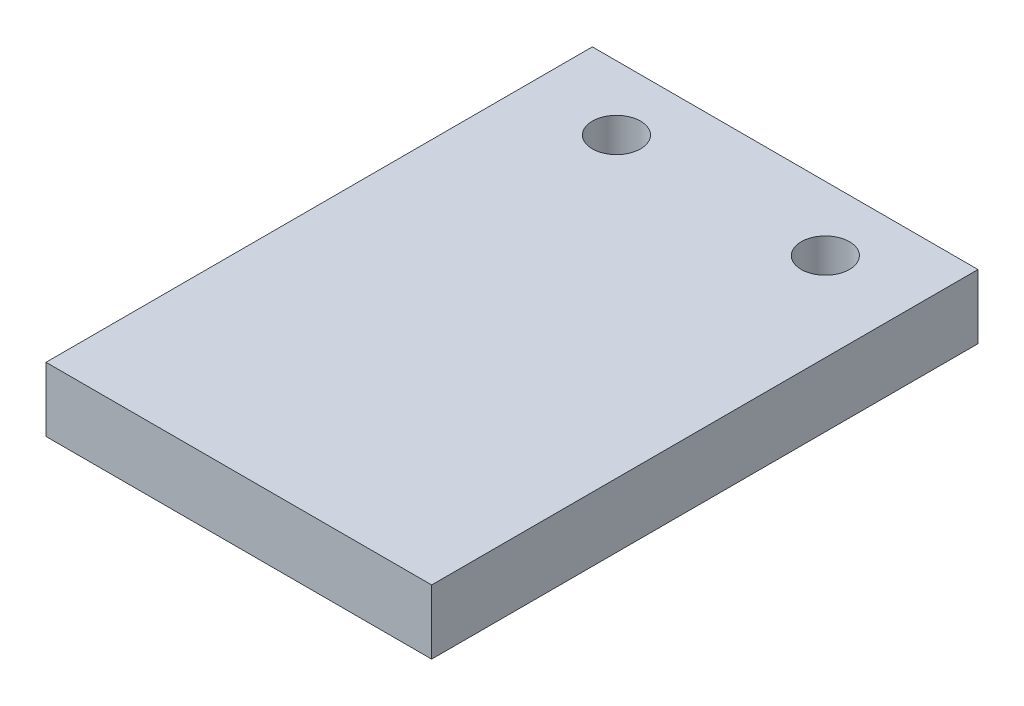
SolidWorks part; units mm, degrees
ref_plane "Front Plane" through (0, 0, 0) normal (0, 0, 1) x (1, 0, 0)
ref_plane "Top Plane" through (0, 0, 0) normal (0, 1, 0) x (1, 0, 0)
ref_plane "Right Plane" through (0, 0, 0) normal (1, 0, 0) x (0, 0, -1)
sketch "Sketch1" plane through (0, 0, 0) normal (0, 1, 0) x (1, 0, 0)
  line L0 (-17.4625, 12.7) -> (58.7375, 12.7)
  line L1 (58.7375, 12.7) -> (58.7375, -95.25)
  line L2 (58.7375, -95.25) -> (-17.4625, -95.25)
  line L3 (-17.4625, -95.25) -> (-17.4625, 12.7)
  circle A0 centre (0, 0) radius 4.7625
  circle A1 centre (41.275, 0) radius 4.7625
extrude "Boss-Extrude1" add sketch "Sketch1" along normal blind 12.7
